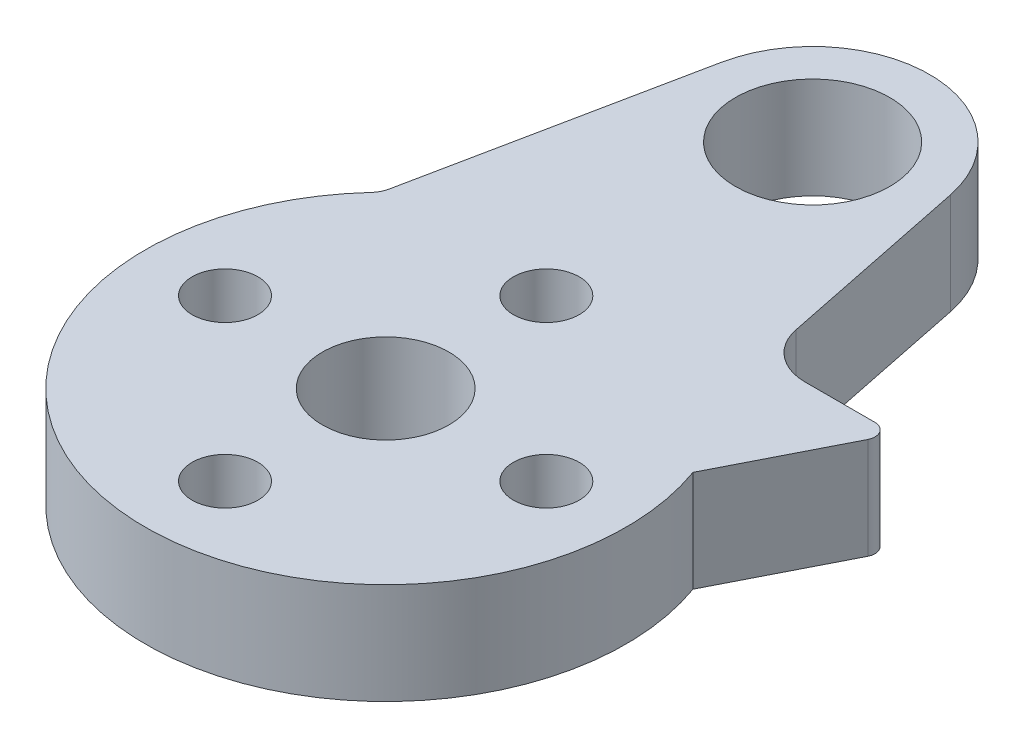
SolidWorks part; units mm, degrees
material "Tough 2000"
ref_plane "Front Plane" through (0, 0, 0) normal (0, 0, 1) x (1, 0, 0)
ref_plane "Top Plane" through (0, 0, 0) normal (0, 1, 0) x (1, 0, 0)
ref_plane "Right Plane" through (0, 0, 0) normal (1, 0, 0) x (0, 0, -1)
sketch "Sketch1" plane through (0, 0, 0) normal (0, 1, 0) x (1, 0, 0)
  line L1 (-4.5316, 17.7996) -> (-7.8384, 1.6)
  line L2 (4.5316, 17.7996) -> (7.8384, 1.6)
  arc A0 (-7.8384, 1.6) -> (7.8384, 1.6) centre (0, 0) ccw
  arc A1 (4.5316, 17.7996) -> (-4.5316, 17.7996) centre (0, 16.8746) ccw
  circle A2 centre (0, 16.8746) radius 3.05
  circle A3 centre (0, 0) radius 2.5
extrude "Boss-Extrude1" add sketch "Sketch1" along normal blind 4
sketch "Sketch2" plane through (0, 4, 0) normal (0, 1, 0) x (1, 0, 0)
  line L0 (0, 0) -> (0, 6.35) construction
  circle A0 centre (0, 6.35) radius 1.3
  circle A1 centre (6.35, 0) radius 1.3
  circle A2 centre (0, -6.35) radius 1.3
  circle A3 centre (-6.35, 0) radius 1.3
  point P13 (0, 0)
  dimension "D1" = 4
extrude "Cut-Extrude1" cut sketch "Sketch2" against normal blind 4
sketch "Sketch3" plane through (0, 4, 0) normal (0, 1, 0) x (1, 0, 0)
  line L0 (-7.8384, 1.6) -> (-6.8137, 6.62)
  line L1 (6.8137, 6.62) -> (7.8384, 1.6)
  line L2 (7.8384, 1.6) -> (4.5316, 17.7996) construction
  arc A1 (-6.8137, 6.62) -> (6.8137, 6.62) centre (0, 0) ccw
  arc A2 (-7.8384, 1.6) -> (7.8384, 1.6) centre (0, 0) ccw construction
  arc A3 (-7.8384, 1.6) -> (7.8384, 1.6) centre (0, 0) ccw
extrude "Boss-Extrude2" add sketch "Sketch3" against normal blind 4
sketch "Sketch4" plane through (0, 4, 0) normal (0, 1, 0) x (1, 0, 0)
  line L7 (10.3923, 8.5104) -> (6.4278, 8.5104)
  line L8 (6.8137, 6.62) -> (4.5316, 17.7996) construction
  line L9 (6.4278, 8.5104) -> (6.8137, 6.62)
  line L10 (6.8137, 6.62) -> (1.7931, 1.7421)
  line L14 (2.1651, 1.25) -> (5.0731, 2.929)
  line L15 (10.3611, 5.9904) -> (11.6423, 8.5104)
  line L16 (11.6423, 8.5104) -> (10.3923, 8.5104)
  line L17 (10.3611, 5.9904) -> (8.9438, 3.2029)
  line L18 (8.9438, 3.2029) -> (5.0731, 2.929)
  arc A3 (2.1651, 1.25) -> (1.7931, 1.7421) centre (0, 0) ccw
  arc A4 (-6.8137, 6.62) -> (6.8137, 6.62) centre (0, 0) ccw construction
extrude "Boss-Extrude3" add sketch "Sketch4" against normal up to surface (4 mm away) up to face at (0, 0, -9.1048)
fillet "Fillet1" radius 1 1 edges at (-6.8137, 2, -6.62)
fillet "Fillet9" radius 0.5 1 edges at (11.6423, 2, -8.5104)
fillet "Fillet10" radius 2 1 edges at (6.4278, 2, -8.5104)
